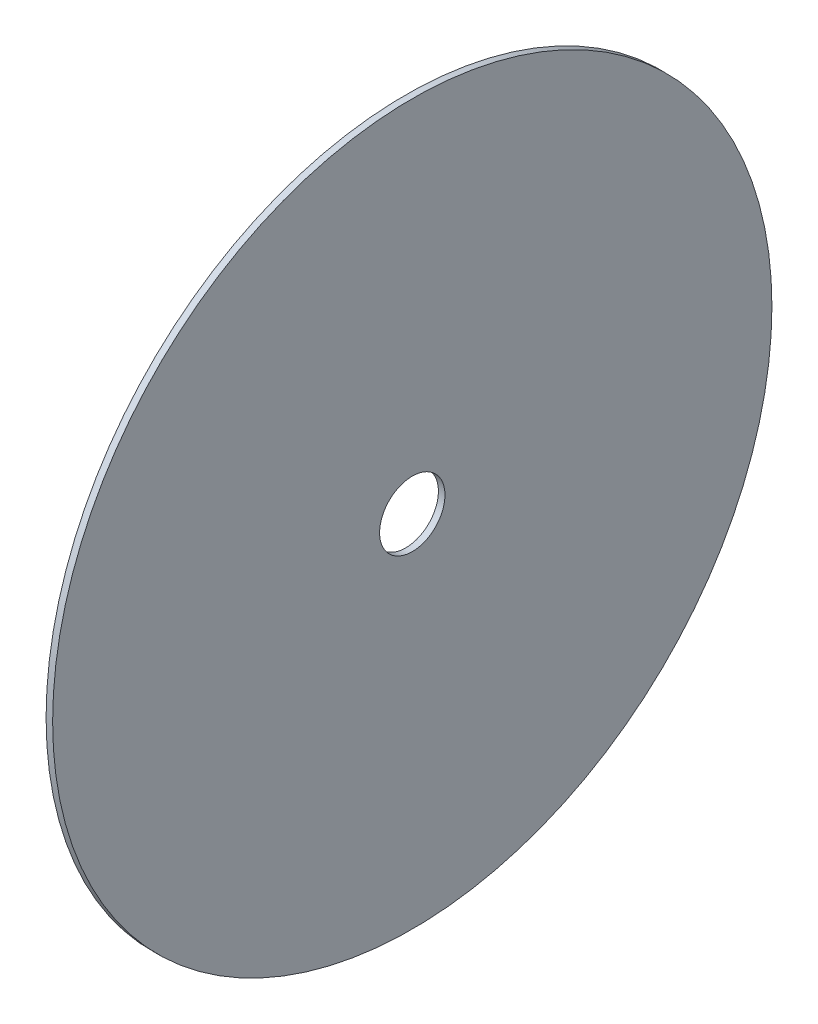
SolidWorks part; units mm, degrees
ref_plane "Спереди" through (0, 0, 0) normal (0, 0, 1) x (1, 0, 0)
ref_plane "Сверху" through (0, 0, 0) normal (0, 1, 0) x (1, 0, 0)
ref_plane "Справа" through (0, 0, 0) normal (1, 0, 0) x (0, 0, -1)
sketch "Эскиз1" plane through (0, 0, 0) normal (1, 0, 0) x (0, 0, -1)
  circle A0 centre (0, 0) radius 110
  circle A1 centre (0, 0) radius 10
extrude "Бобышка-Вытянуть1" add sketch "Эскиз1" along normal blind 2
